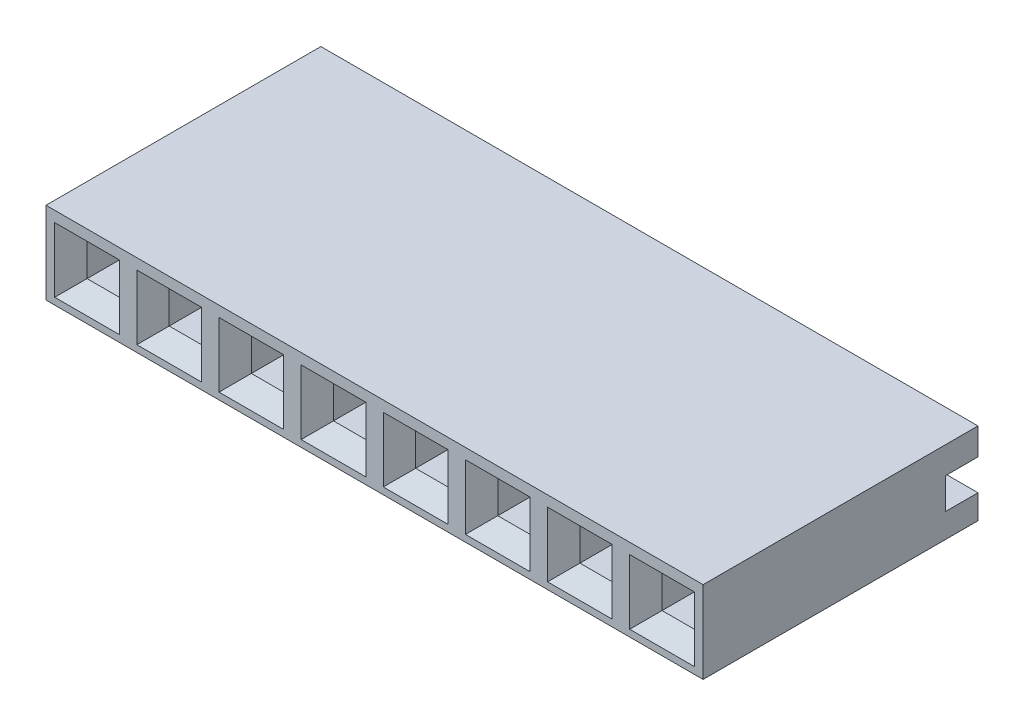
SolidWorks part; units mm, degrees
material "ABS"
ref_plane "Front Plane" through (0, 0, 0) normal (0, 0, 1) x (1, 0, 0)
ref_plane "Top Plane" through (0, 0, 0) normal (0, 1, 0) x (1, 0, 0)
ref_plane "Right Plane" through (0, 0, 0) normal (1, 0, 0) x (0, 0, -1)
sketch "Sketch1" plane through (0, 0, 0) normal (1, 0, 0) x (0, 0, -1)
  line L16 (8.5, 2.54) -> (0, 2.54)
  line L17 (0, 2.54) -> (0, 0)
  line L18 (0, 0) -> (8.5, 0)
  line L19 (8.5, 0) -> (8.5, 0.75)
  line L20 (8.5, 0.75) -> (7.5, 0.75)
  line L21 (7.5, 0.75) -> (7.5, 1.71)
  line L22 (7.5, 1.71) -> (8.5, 1.71)
  line L23 (8.5, 1.71) -> (8.5, 2.54)
  dimension "D1" = 0.83
  dimension "D2" = 0.75
  dimension "D3" = 1
  dimension "D4" = 8.5
  dimension "D5" = 2.54
extrude "Boss-Extrude1" add sketch "Sketch1" against normal blind 20.32 separate body
sketch "Sketch2" plane through (0, 0, -7.5) normal (0, 0, -1) x (-1, 0, 0)
  line L3 (2.27, 1.11) -> (2.27, 1.71)
  line L4 (2.27, 1.11) -> (0.27, 1.11)
  line L5 (0.27, 1.11) -> (0.27, 1.71)
  line L6 (2.27, 1.71) -> (0.27, 1.71)
  line L7 (20.32, 1.71) -> (0, 1.71) construction
  line L8 (0, 0.75) -> (0, 1.71) construction
  dimension "D1" = 0.6
  dimension "D2" = 0.27
  dimension "D3" = 2
extrude "Cut-Extrude1" cut sketch "Sketch2" against normal blind 5.5
sketch "Sketch3" plane through (0, 0, 0) normal (0, 0, -1) x (-1, 0, 0)
  line L4 (0.77, 1.71) -> (1.77, 1.71)
  line L5 (0.77, 0.71) -> (0.77, 1.71)
  line L6 (1.77, 0.71) -> (0.77, 0.71)
  line L7 (1.77, 1.71) -> (1.77, 0.71)
  line L8 (2.27, 1.71) -> (0.27, 1.71) construction
  line L9 (0, 0.75) -> (0, 1.71) construction
  dimension "D1" = 1
  dimension "D2" = 0.77
extrude "Cut-Extrude2" cut sketch "Sketch3" along normal blind 6
sketch "Sketch4" plane through (0, 0, 0) normal (0, 0, 1) x (1, 0, 0)
  line L8 (-2.27, 2.21) -> (-2.27, 0.21)
  line L9 (-2.27, 0.21) -> (-0.27, 0.21)
  line L10 (-0.27, 0.21) -> (-0.27, 2.21)
  line L11 (-0.27, 2.21) -> (-2.27, 2.21)
  line L12 (-2.27, 2.21) -> (-2.27, 0.21)
  line L13 (-2.27, 0.21) -> (-0.27, 0.21)
  line L14 (-0.27, 0.21) -> (-0.27, 2.21)
  line L15 (-0.27, 2.21) -> (-2.27, 2.21)
  dimension "D1" = 0.5
extrude "Cut-Extrude3" cut sketch "Sketch4" against normal blind 0.5 draft 45
pattern_linear "LPattern1" count 8 spacing 2.54 along (-1, 0, 0) of "Cut-Extrude2", "Cut-Extrude1", "Cut-Extrude3"
sketch "Sketch6" plane through (0, 0, -8.5) normal (0, 0, -1) x (-1, 0, 0)
  line L0 (20.32, 2.54) -> (0, 2.54) construction
  line L1 (20.32, 0) -> (0, 0) construction
  line L2 (20.32, 2.54) -> (0, 2.54)
  line L3 (20.32, 0) -> (0, 0)
  line L4 (20.32, 2.54) -> (0, 0) construction
  point P4 (10.16, 1.27)
